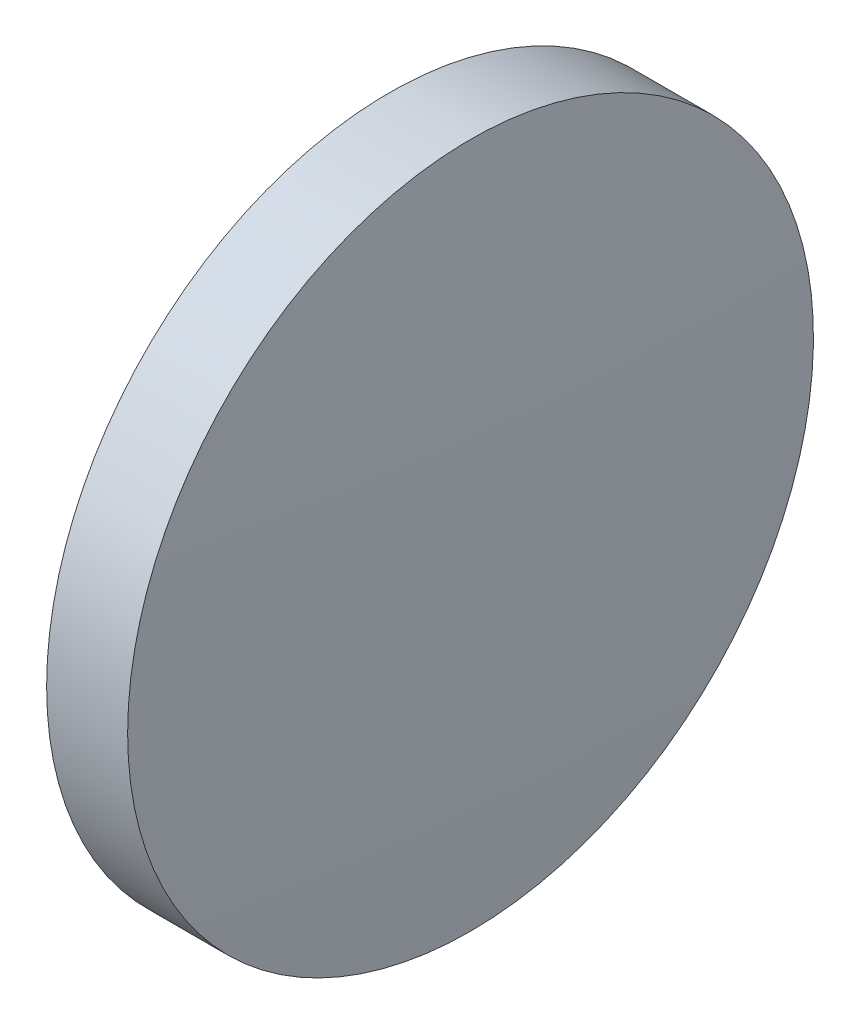
SolidWorks part; units mm, degrees
ref_plane "前视基准面" through (0, 0, 0) normal (0, 0, 1) x (1, 0, 0)
ref_plane "上视基准面" through (0, 0, 0) normal (0, 1, 0) x (1, 0, 0)
ref_plane "右视基准面" through (0, 0, 0) normal (1, 0, 0) x (0, 0, -1)
sketch "草图1" plane through (0, 0, 0) normal (0, 0, 1) x (1, 0, 0)
  line L0 (110.1654, 65.2336) -> (128.9614, 65.2336) construction
  line L1 (115.7736, 65.2336) -> (115.7736, 77.9336)
  line L2 (115.7736, 77.9336) -> (118.7739, 77.9336)
  line L3 (119.1256, 65.2336) -> (115.7736, 65.2336)
  arc A0 (119.1256, 65.2336) -> (118.7739, 77.9336) centre (-110.3744, 65.2336) ccw
  dimension "D1" = 229.5
revolve "旋转1" add sketch "草图1" angle 360 about L0
